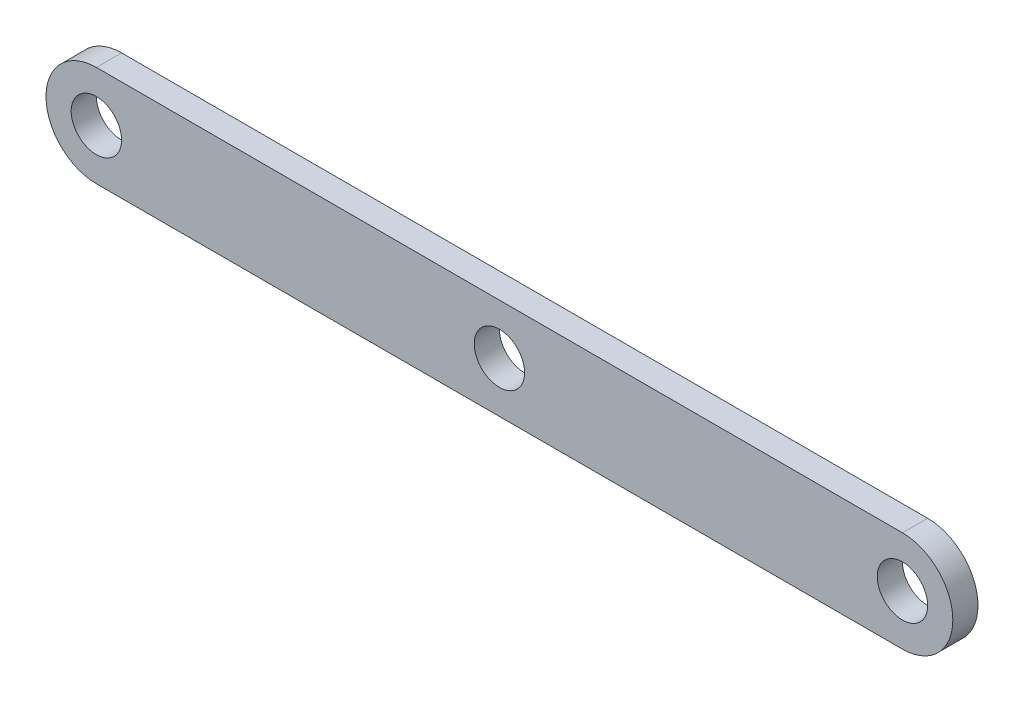
SolidWorks part; units mm, degrees
ref_plane "Front Plane" through (0, 0, 0) normal (0, 0, 1) x (1, 0, 0)
ref_plane "Top Plane" through (0, 0, 0) normal (0, 1, 0) x (1, 0, 0)
ref_plane "Right Plane" through (0, 0, 0) normal (1, 0, 0) x (0, 0, -1)
sketch "Sketch1" plane through (0, 0, 0) normal (0, 0, 1) x (1, 0, 0)
  line L0 (0, 6.35) -> (101.6, 6.35)
  line L1 (0, -6.35) -> (101.6, -6.35)
  arc A0 (0, 6.35) -> (0, -6.35) centre (0, 0) ccw
  arc A1 (101.6, -6.35) -> (101.6, 6.35) centre (101.6, 0) ccw
  circle A2 centre (0, 0) radius 3.175
  circle A3 centre (101.6, 0) radius 3.175
  circle A4 centre (50.8, 0) radius 3.175
  dimension "D1" = 12.7
  dimension "D4" = 6.35
  dimension "D5" = 6.35
  dimension "D6" = 6.35
  dimension "D2" = 101.6
  dimension "D3" = 101.6
extrude "Boss-Extrude1" add sketch "Sketch1" along normal blind 3.175
